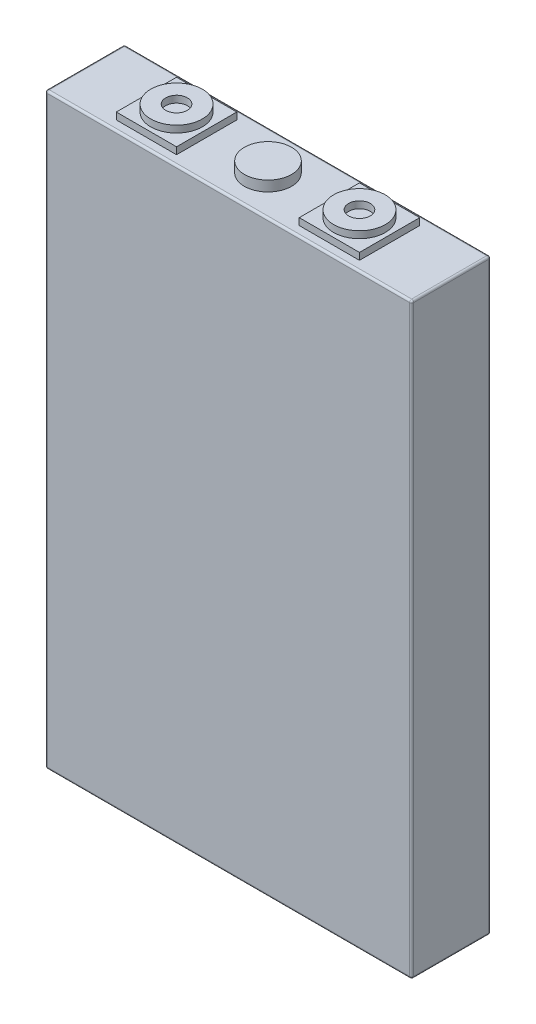
SolidWorks part; units mm, degrees
ref_plane "Front Plane" through (0, 0, 0) normal (0, 0, 1) x (1, 0, 0)
ref_plane "Top Plane" through (0, 0, 0) normal (0, 1, 0) x (1, 0, 0)
ref_plane "Right Plane" through (0, 0, 0) normal (1, 0, 0) x (0, 0, -1)
sketch "Sketch1" plane through (0, 0, 0) normal (0, 1, 0) x (1, 0, 0)
  line L1 (0, 0) -> (135.2, 0)
  line L2 (0, 0) -> (0, 29.2)
  line L3 (0, 29.2) -> (135.2, 29.2)
  line L4 (135.2, 0) -> (135.2, 29.2)
  dimension "D1" = 135.2
  dimension "D2" = 29.2
extrude "Boss-Extrude1" add sketch "Sketch1" along normal blind 216.8
sketch "Sketch2" plane through (0, 216.8, 0) normal (0, 1, 0) x (1, 0, 0)
  line L0 (67.6, 29.2) -> (67.6, 0) construction
  line L1 (135.2, 29.2) -> (0, 29.2) construction
  line L2 (0, 0) -> (135.2, 0) construction
  line L3 (33.85, 14.6) -> (101.35, 14.6) construction
  line L5 (44.9625, 25.7125) -> (22.7375, 25.7125)
  line L6 (44.9625, 25.7125) -> (44.9625, 3.4875)
  line L7 (44.9625, 3.4875) -> (22.7375, 3.4875)
  line L8 (22.7375, 25.7125) -> (22.7375, 3.4875)
  line L9 (44.9625, 25.7125) -> (22.7375, 3.4875) construction
  line L10 (44.9625, 3.4875) -> (22.7375, 25.7125) construction
  line L11 (90.2375, 25.7125) -> (112.4625, 25.7125)
  line L12 (90.2375, 25.7125) -> (90.2375, 3.4875)
  line L13 (90.2375, 3.4875) -> (112.4625, 3.4875)
  line L14 (112.4625, 25.7125) -> (112.4625, 3.4875)
  line L15 (90.2375, 25.7125) -> (112.4625, 3.4875) construction
  line L16 (90.2375, 3.4875) -> (112.4625, 25.7125) construction
  point P8 (67.6, 14.6)
  point P9 (67.6, 14.6)
  dimension "D1" = 67.5
  dimension "D2" = 22.225
  dimension "D3" = 22.225
  dimension "D4" = 22.225
  dimension "D5" = 22.225
extrude "Boss-Extrude2" add sketch "Sketch2" along normal blind 2.54 separate body
sketch "Sketch4" plane through (0, 219.34, 0) normal (0, 1, 0) x (1, 0, 0)
  line L0 (22.7375, 3.4875) -> (44.9625, 25.7125) construction
  line L1 (44.9625, 25.7125) -> (22.7375, 25.7125) construction
  line L2 (90.2375, 25.7125) -> (112.4625, 3.4875) construction
  circle A0 centre (33.85, 14.6) radius 9.525
  circle A1 centre (101.35, 14.6) radius 9.525
  circle A2 centre (33.85, 14.6) radius 4
  circle A3 centre (101.35, 14.6) radius 4
  dimension "D1" = 8
  dimension "D2" = 19.05
  dimension "D3" = 19.05
  dimension "D4" = 8
extrude "Boss-Extrude3" add sketch "Sketch4" along normal blind 2.54 separate body
sketch "Sketch5" plane through (0, 216.8, 0) normal (0, 1, 0) x (1, 0, 0)
  line L0 (67.6, 29.2) -> (67.6, 0) construction
  line L1 (135.2, 29.2) -> (0, 29.2) construction
  line L2 (0, 0) -> (135.2, 0) construction
  circle A0 centre (67.6, 14.6) radius 8.6981
extrude "Boss-Extrude4" add sketch "Sketch5" along normal blind 3.81 separate body
fillet "Fillet1" radius 0.762 12 edges at (67.6, 216.8, -29.2) (67.6, 0, -29.2) (135.2, 216.8, -14.6) (135.2, 108.4, -29.2) (135.2, 0, -14.6) (67.6, 216.8, 0) (135.2, 108.4, 0) (67.6, 0, 0) (0, 108.4, -29.2) (0, 216.8, -14.6) (0, 108.4, 0) (0, 0, -14.6)
